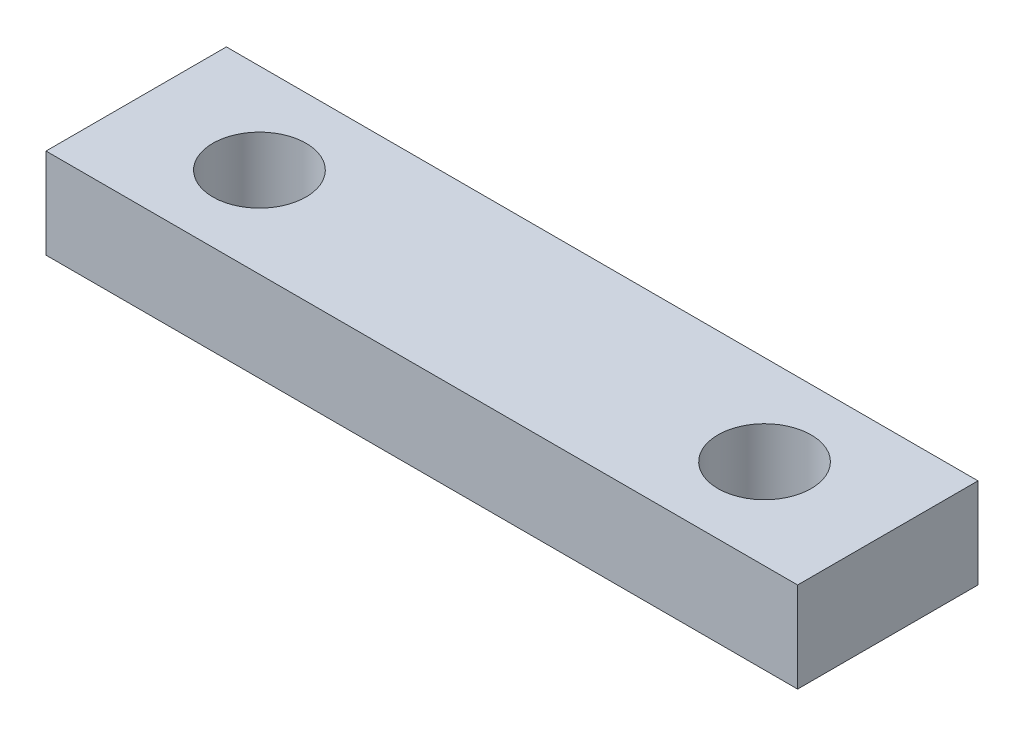
SolidWorks part; units mm, degrees
ref_plane "Front Plane" through (0, 0, 0) normal (0, 0, 1) x (1, 0, 0)
ref_plane "Top Plane" through (0, 0, 0) normal (0, 1, 0) x (1, 0, 0)
ref_plane "Right Plane" through (0, 0, 0) normal (1, 0, 0) x (0, 0, -1)
sketch "Sketch1" plane through (0, 0, 0) normal (0, 1, 0) x (1, 0, 0)
  line L1 (-12.5, 3) -> (12.5, 3)
  line L2 (-12.5, 3) -> (-12.5, -3)
  line L3 (-12.5, -3) -> (12.5, -3)
  line L4 (12.5, 3) -> (12.5, -3)
  line L5 (-12.5, 3) -> (12.5, -3) construction
  line L6 (-12.5, -3) -> (12.5, 3) construction
  circle A0 centre (-8.4, 0) radius 1.55
  circle A1 centre (8.4, 0) radius 1.55
  point P0 (0, 0)
  dimension "D3" = 3.1
  dimension "D4" = 3.1
  dimension "D5" = 16.8
  dimension "D6" = 8.4
  dimension "D1" = 25
  dimension "D2" = 6
extrude "Boss-Extrude1" add sketch "Sketch1" along normal blind 3
